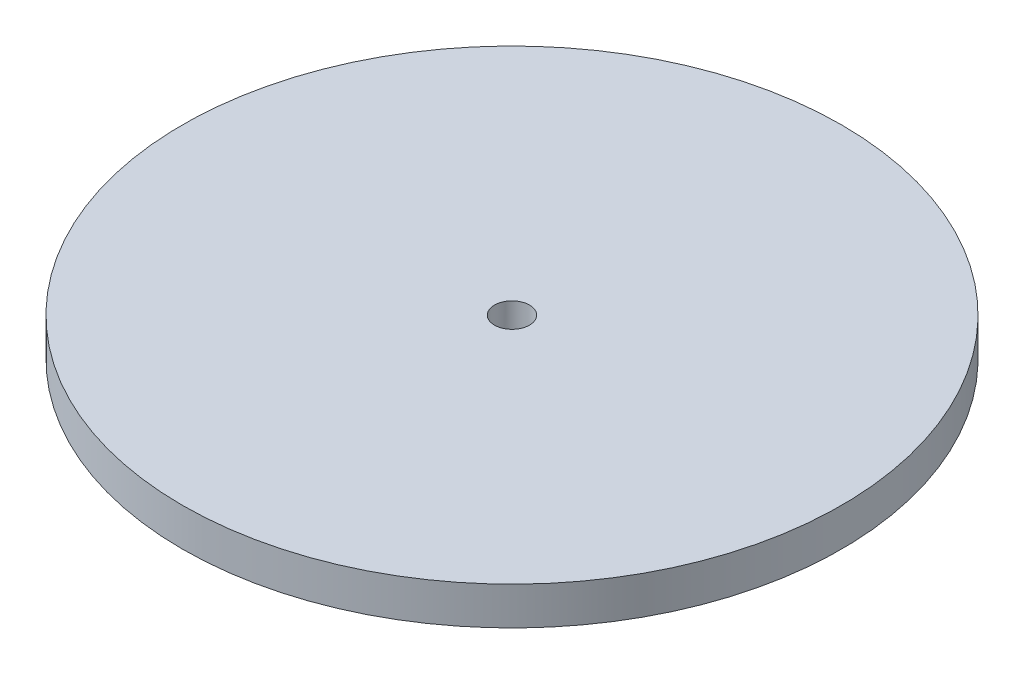
SolidWorks part; units mm, degrees
material "6061-T6 (SS)"
ref_plane "Front Plane" through (0, 0, 0) normal (0, 0, 1) x (1, 0, 0)
ref_plane "Top Plane" through (0, 0, 0) normal (0, 1, 0) x (1, 0, 0)
ref_plane "Right Plane" through (0, 0, 0) normal (1, 0, 0) x (0, 0, -1)
sketch "Sketch1" plane through (0, 0, 0) normal (0, 1, 0) x (1, 0, 0)
  circle A0 centre (0, 0) radius 83.82
  dimension "D1" = 167.64
extrude "Boss-Extrude1" add sketch "Sketch1" along normal mid plane 9.652
sketch "Sketch2" plane through (0, 0, 0) normal (0, 0, 1) x (1, 0, 0)
  line L0 (0, -18.3275) -> (0, 20.8308) construction
  line L1 (0, -4.826) -> (-19.297, -4.826)
  line L2 (-83.82, -4.826) -> (83.82, -4.826) construction
  line L3 (0, -4.826) -> (0, -1.4952)
  line L4 (-0.3818, -1.4952) -> (0, -1.4952)
  arc A0 (-19.297, -4.826) -> (-0.3818, -1.4952) centre (-0.4072, -56.7254) cw
  dimension "D6" = 55.2302
  dimension "D1" = 19.297
  dimension "D2" = 3.3308
  dimension "D3" = 0.3818
revolve "Cut-Revolve1" cut sketch "Sketch2" angle 360 about L0
sketch "Sketch3" plane through (0, 4.826, 0) normal (0, 1, 0) x (1, 0, 0)
  circle A0 centre (0, 0) radius 4.445
  dimension "D1" = 8.89
extrude "Cut-Extrude1" cut sketch "Sketch3" against normal up to surface (9.652 mm away) up to face at (0, -4.826, -19.297)
